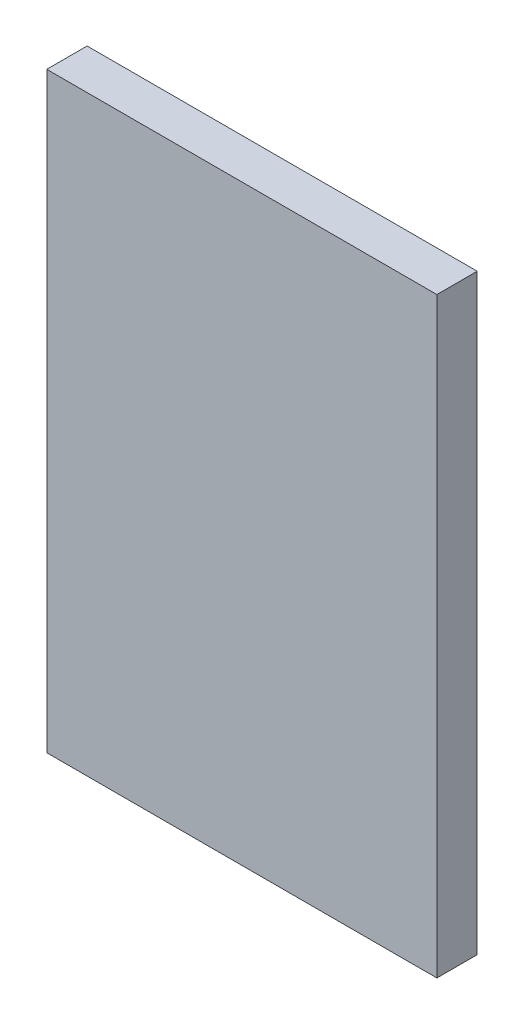
SolidWorks part; units mm, degrees
material "Oak"
ref_plane "Front Plane" through (0, 0, 0) normal (0, 0, 1) x (1, 0, 0)
ref_plane "Top Plane" through (0, 0, 0) normal (0, 1, 0) x (1, 0, 0)
ref_plane "Right Plane" through (0, 0, 0) normal (1, 0, 0) x (0, 0, -1)
sketch "Sketch1" plane through (0, 0, 0) normal (0, 0, 1) x (1, 0, 0)
  line L1 (-92.075, -139.7) -> (92.075, -139.7)
  line L2 (-92.075, -139.7) -> (-92.075, 139.7)
  line L3 (-92.075, 139.7) -> (92.075, 139.7)
  line L4 (92.075, -139.7) -> (92.075, 139.7)
  line L5 (-92.075, -139.7) -> (92.075, 139.7) construction
  line L6 (-92.075, 139.7) -> (92.075, -139.7) construction
  point P0 (0, 0)
  dimension "D1" = 279.4
  dimension "D2" = 184.15
extrude "Boss-Extrude1" add sketch "Sketch1" along normal blind 19.05
